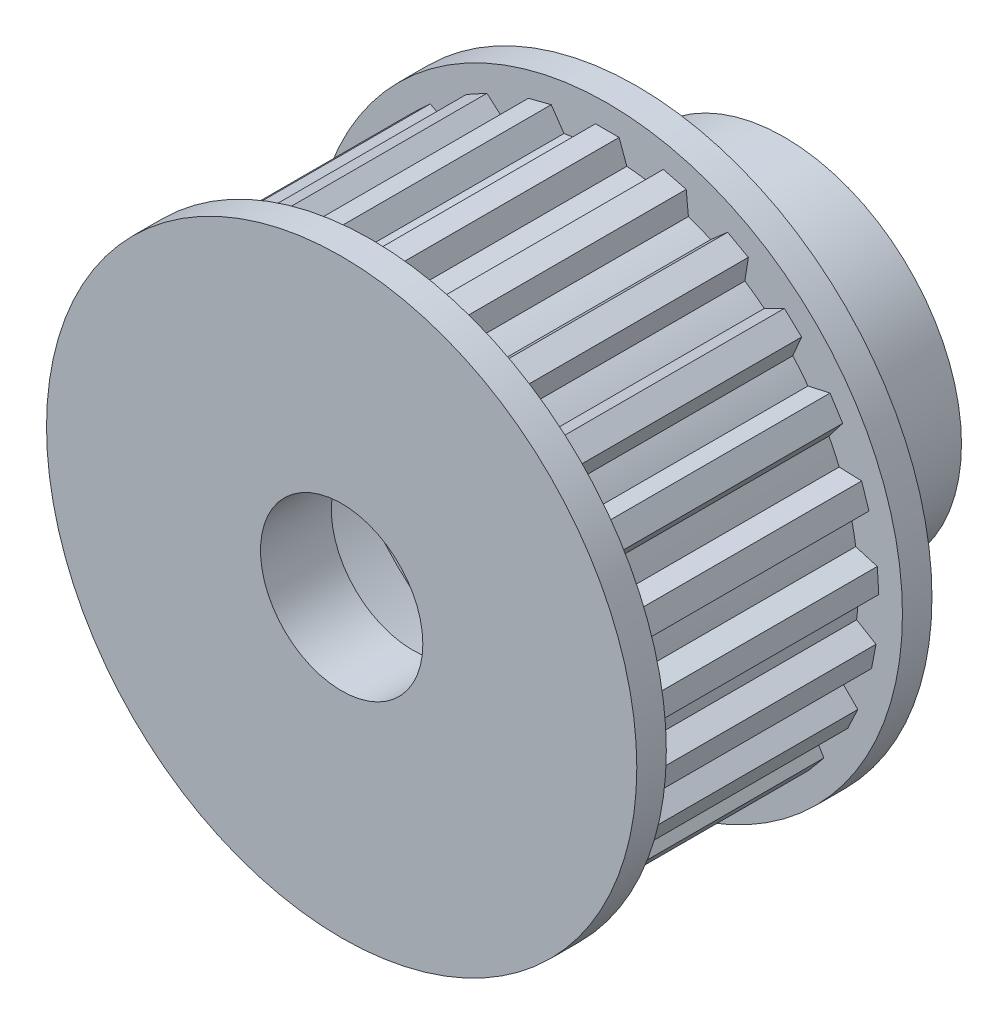
SolidWorks part; units mm, degrees
ref_plane "Front Plane" through (0, 0, 0) normal (0, 0, 1) x (1, 0, 0)
ref_plane "Top Plane" through (0, 0, 0) normal (0, 1, 0) x (1, 0, 0)
ref_plane "Right Plane" through (0, 0, 0) normal (1, 0, 0) x (0, 0, -1)
sketch "Sketch1" plane through (0, 0, 0) normal (0, 0, 1) x (1, 0, 0)
  line L0 (-0.4, 9.1913) -> (-0.661, 8.4743)
  line L1 (-0.4, 9.1913) -> (0.4, 9.1913)
  line L2 (0.4, 9.1913) -> (0.661, 8.4743)
  line L3 (0, 9.2) -> (0, -9.2) construction
  line L4 (1.8984, 9.002) -> (1.4672, 8.3724)
  line L5 (1.8984, 9.002) -> (2.6732, 8.8031)
  line L6 (2.6732, 8.8031) -> (2.7477, 8.0436)
  line L7 (4.0774, 8.2471) -> (3.5033, 7.7445)
  line L8 (4.0774, 8.2471) -> (4.7785, 7.8617)
  line L9 (4.7785, 7.8617) -> (4.6617, 7.1076)
  line L10 (6.0003, 6.974) -> (5.3192, 6.6299)
  line L11 (6.0003, 6.974) -> (6.5835, 6.4264)
  line L12 (6.5835, 6.4264) -> (6.2829, 5.725)
  line L13 (7.5461, 5.2627) -> (6.8009, 5.0988)
  line L14 (7.5461, 5.2627) -> (7.9748, 4.5872)
  line L15 (7.9748, 4.5872) -> (7.5092, 3.9827)
  line L16 (8.6178, 3.2207) -> (7.8552, 3.2473)
  line L17 (8.6178, 3.2207) -> (8.8651, 2.4598)
  line L18 (8.8651, 2.4598) -> (8.2638, 1.9901)
  line L19 (9.148, 0.9763) -> (8.416, 1.1918)
  line L20 (9.148, 0.9763) -> (9.1983, 0.1779)
  line L21 (9.1983, 0.1779) -> (8.499, -0.1276)
  line L22 (9.1034, -1.3294) -> (8.448, -0.9386)
  line L23 (9.1034, -1.3294) -> (8.9535, -2.1152)
  line L24 (8.9535, -2.1152) -> (8.2003, -2.2372)
  line L25 (8.4868, -3.5515) -> (7.9492, -3.0101)
  line L26 (8.4868, -3.5515) -> (8.1462, -4.2754)
  line L27 (8.1462, -4.2754) -> (7.3863, -4.2062)
  line L28 (7.337, -5.5505) -> (6.9509, -4.8924)
  line L29 (7.337, -5.5505) -> (6.827, -6.167)
  line L30 (6.827, -6.167) -> (6.1082, -5.911)
  line L31 (5.7261, -7.2008) -> (5.5158, -6.4673)
  line L32 (5.7261, -7.2008) -> (5.0789, -7.671)
  line L33 (5.0789, -7.671) -> (4.4463, -7.2443)
  line L34 (3.7555, -8.3986) -> (3.7341, -7.6358)
  line L35 (3.7555, -8.3986) -> (3.0116, -8.6931)
  line L36 (3.0116, -8.6931) -> (2.505, -8.1225)
  line L37 (1.5488, -9.0687) -> (1.7179, -8.3246)
  line L38 (1.5488, -9.0687) -> (0.7551, -9.169)
  line L39 (0.7551, -9.169) -> (0.4063, -8.4903)
  line L40 (-0.7551, -9.169) -> (-0.4063, -8.4903)
  line L41 (-0.7551, -9.169) -> (-1.5488, -9.0687)
  line L42 (-1.5488, -9.0687) -> (-1.7179, -8.3246)
  line L43 (-3.0116, -8.6931) -> (-2.505, -8.1225)
  line L44 (-3.0116, -8.6931) -> (-3.7555, -8.3986)
  line L45 (-3.7555, -8.3986) -> (-3.7341, -7.6358)
  line L46 (-5.0789, -7.671) -> (-4.4463, -7.2443)
  line L47 (-5.0789, -7.671) -> (-5.7261, -7.2008)
  line L48 (-5.7261, -7.2008) -> (-5.5158, -6.4673)
  line L49 (-6.827, -6.167) -> (-6.1082, -5.911)
  line L50 (-6.827, -6.167) -> (-7.337, -5.5505)
  line L51 (-7.337, -5.5505) -> (-6.9509, -4.8924)
  line L52 (-8.1462, -4.2754) -> (-7.3863, -4.2062)
  line L53 (-8.1462, -4.2754) -> (-8.4868, -3.5515)
  line L54 (-8.4868, -3.5515) -> (-7.9492, -3.0101)
  line L55 (-8.9535, -2.1152) -> (-8.2003, -2.2372)
  line L56 (-8.9535, -2.1152) -> (-9.1034, -1.3294)
  line L57 (-9.1034, -1.3294) -> (-8.448, -0.9386)
  line L58 (-9.1983, 0.1779) -> (-8.499, -0.1276)
  line L59 (-9.1983, 0.1779) -> (-9.148, 0.9763)
  line L60 (-9.148, 0.9763) -> (-8.416, 1.1918)
  line L61 (-8.8651, 2.4598) -> (-8.2638, 1.9901)
  line L62 (-8.8651, 2.4598) -> (-8.6178, 3.2207)
  line L63 (-8.6178, 3.2207) -> (-7.8552, 3.2473)
  line L64 (-7.9748, 4.5872) -> (-7.5092, 3.9827)
  line L65 (-7.9748, 4.5872) -> (-7.5461, 5.2627)
  line L66 (-7.5461, 5.2627) -> (-6.8009, 5.0988)
  line L67 (-6.5835, 6.4264) -> (-6.2829, 5.725)
  line L68 (-6.5835, 6.4264) -> (-6.0003, 6.974)
  line L69 (-6.0003, 6.974) -> (-5.3192, 6.6299)
  line L70 (-4.7785, 7.8617) -> (-4.6617, 7.1076)
  line L71 (-4.7785, 7.8617) -> (-4.0774, 8.2471)
  line L72 (-4.0774, 8.2471) -> (-3.5033, 7.7445)
  line L73 (-2.6732, 8.8031) -> (-2.7477, 8.0436)
  line L74 (-2.6732, 8.8031) -> (-1.8984, 9.002)
  line L75 (-1.8984, 9.002) -> (-1.4672, 8.3724)
  arc A0 (1.4672, 8.3724) -> (0.661, 8.4743) centre (0, 0) ccw
  arc A2 (3.5033, 7.7445) -> (2.7477, 8.0436) centre (0, 0) ccw
  arc A3 (5.3192, 6.6299) -> (4.6617, 7.1076) centre (0, 0) ccw
  arc A4 (6.8009, 5.0988) -> (6.2829, 5.725) centre (0, 0) ccw
  arc A5 (7.8552, 3.2473) -> (7.5092, 3.9827) centre (0, 0) ccw
  arc A6 (8.416, 1.1918) -> (8.2638, 1.9901) centre (0, 0) ccw
  arc A7 (8.448, -0.9386) -> (8.499, -0.1276) centre (0, 0) ccw
  arc A8 (7.9492, -3.0101) -> (8.2003, -2.2372) centre (0, 0) ccw
  arc A9 (6.9509, -4.8924) -> (7.3863, -4.2062) centre (0, 0) ccw
  arc A10 (5.5158, -6.4673) -> (6.1082, -5.911) centre (0, 0) ccw
  arc A11 (3.7341, -7.6358) -> (4.4463, -7.2443) centre (0, 0) ccw
  arc A12 (1.7179, -8.3246) -> (2.505, -8.1225) centre (0, 0) ccw
  arc A13 (-0.4063, -8.4903) -> (0.4063, -8.4903) centre (0, 0) ccw
  arc A14 (-2.505, -8.1225) -> (-1.7179, -8.3246) centre (0, 0) ccw
  arc A15 (-4.4463, -7.2443) -> (-3.7341, -7.6358) centre (0, 0) ccw
  arc A16 (-6.1082, -5.911) -> (-5.5158, -6.4673) centre (0, 0) ccw
  arc A17 (-7.3863, -4.2062) -> (-6.9509, -4.8924) centre (0, 0) ccw
  arc A18 (-8.2003, -2.2372) -> (-7.9492, -3.0101) centre (0, 0) ccw
  arc A19 (-8.499, -0.1276) -> (-8.448, -0.9386) centre (0, 0) ccw
  arc A20 (-8.2638, 1.9901) -> (-8.416, 1.1918) centre (0, 0) ccw
  arc A21 (-7.5092, 3.9827) -> (-7.8552, 3.2473) centre (0, 0) ccw
  arc A22 (-6.2829, 5.725) -> (-6.8009, 5.0988) centre (0, 0) ccw
  arc A23 (-4.6617, 7.1076) -> (-5.3192, 6.6299) centre (0, 0) ccw
  arc A24 (-2.7477, 8.0436) -> (-3.5033, 7.7445) centre (0, 0) ccw
  arc A25 (-0.661, 8.4743) -> (-1.4672, 8.3724) centre (0, 0) ccw
  point P109 (0, 0)
  dimension "D1" = 17
  dimension "D3" = 0.8
  dimension "D4" = 40
  dimension "D5" = 25
extrude "Boss-Extrude1" add sketch "Sketch1" along normal mid plane 10
sketch "Sketch2" plane through (0, 0, 5) normal (0, 0, 1) x (1, 0, 0)
  circle A0 centre (0, 0) radius 10
  dimension "D1" = 20
extrude "Boss-Extrude2" add sketch "Sketch2" against normal blind 1
mirror "Mirror1" about plane through (0, 0, 0) normal (0, 0, 1) of "Boss-Extrude2"
sketch "Sketch4" plane through (0, 0, -5) normal (0, 0, -1) x (-1, 0, 0)
  circle A0 centre (0, 0) radius 6
  dimension "D1" = 12
extrude "Boss-Extrude3" add sketch "Sketch4" along normal blind 5
sketch "Sketch5" plane through (0, 0, 5) normal (0, 0, 1) x (1, 0, 0)
  circle A0 centre (0, 0) radius 2.75
  dimension "D1" = 5.5
extrude "Cut-Extrude1" cut sketch "Sketch5" against normal up to next
sketch "Sketch7" plane through (0, 0, 0) normal (0, 0, 1) x (1, 0, 0)
  circle A0 centre (0, 0) radius 8.1
  dimension "D1" = 16.2
extrude "Cut-Extrude2" cut sketch "Sketch7" against normal mid plane 5.2
equation "\"d1\"= 16"
